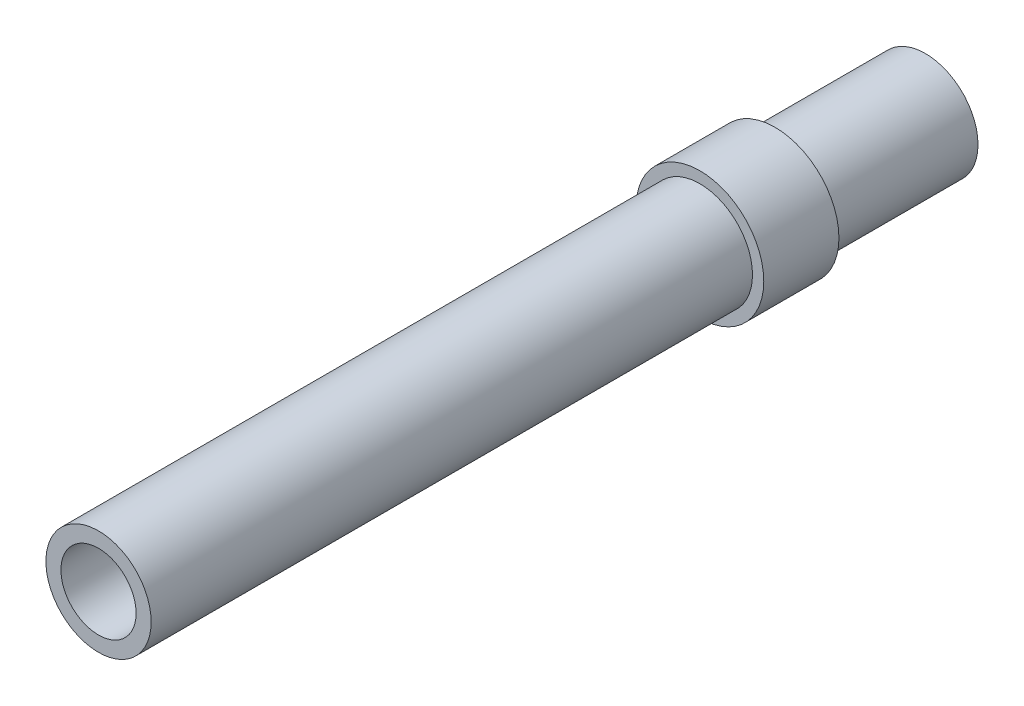
SolidWorks part; units mm, degrees
ref_plane "Ön Düzlem" through (0, 0, 0) normal (0, 0, 1) x (1, 0, 0)
ref_plane "Üst Düzlem" through (0, 0, 0) normal (0, 1, 0) x (1, 0, 0)
ref_plane "Sağ Düzlem" through (0, 0, 0) normal (1, 0, 0) x (0, 0, -1)
sketch "Çizim1" plane through (0, 0, 0) normal (0, 0, 1) x (1, 0, 0)
  circle A0 centre (0, 0) radius 2.5
  circle A1 centre (0, 0) radius 3.5
  dimension "D1" = 5
  dimension "D2" = 7
extrude "Yükseklik-Ekstrüzyon1" add sketch "Çizim1" along normal blind 50
sketch "Çizim2" plane through (0, 0, 50) normal (0, 0, 1) x (1, 0, 0)
  circle A0 centre (0, 0) radius 3.5 construction
  circle A1 centre (0, 0) radius 3.5
extrude "Yükseklik-Ekstrüzyon2" add sketch "Çizim2" along normal blind 5
ref_plane "Düzlem1" through (0, 0, 10) normal (0, 0, 1) x (1, 0, 0)
sketch "Çizim3" plane through (0, 0, 10) normal (0, 0, 1) x (1, 0, 0)
  circle A0 centre (0, 0) radius 4.25
  dimension "D1" = 8.5
extrude "Yükseklik-Ekstrüzyon3" add sketch "Çizim3" along normal blind 5
sketch "Çizim5" plane through (0, 0, 10) normal (0, 0, -1) x (-1, 0, 0)
  circle A0 centre (0, 0) radius 2.5 construction
  circle A1 centre (0, 0) radius 2.5
extrude "Kes-Ekstrüzyon1" cut sketch "Çizim5" against normal blind 60
